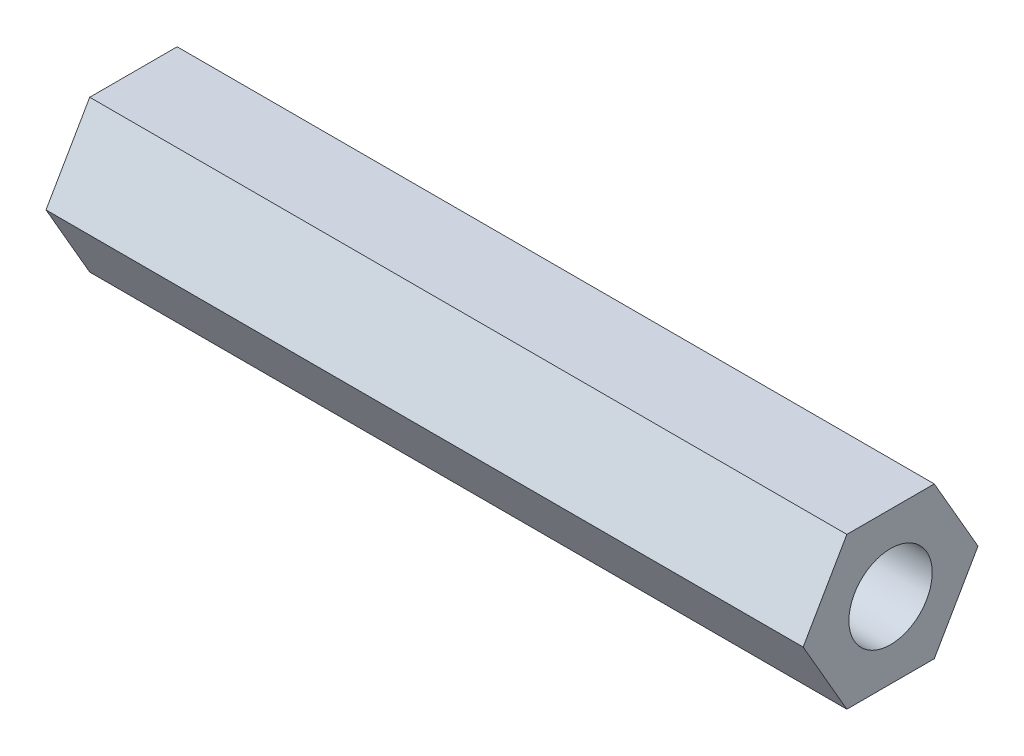
SolidWorks part; units mm, degrees
ref_plane "前视基准面" through (0, 0, 0) normal (0, 0, 1) x (1, 0, 0)
ref_plane "上视基准面" through (0, 0, 0) normal (0, 1, 0) x (1, 0, 0)
ref_plane "右视基准面" through (0, 0, 0) normal (1, 0, 0) x (0, 0, -1)
other "Configuration Table"
sketch "草图1" plane through (0, 0, 0) normal (1, 0, 0) x (0, 0, -1)
  line L1 (3.4641, 0) -> (1.7321, 3)
  line L2 (1.7321, 3) -> (-1.7321, 3)
  line L3 (-1.7321, 3) -> (-3.4641, 0)
  line L4 (-3.4641, 0) -> (-1.7321, -3)
  line L5 (-1.7321, -3) -> (1.7321, -3)
  line L6 (1.7321, -3) -> (3.4641, 0)
  circle A0 centre (0, 0) radius 3 construction
  dimension "D1" = 6
extrude "凸台-拉伸1" add sketch "草图1" along normal blind 30
hole_wizard "M4 螺纹孔1" positions "草图3" profile "草图4" tap size "M4" standard "GB" end condition through all
sketch "草图3" plane through (0, 0, 0) normal (-1, 0, 0) x (0, 0, 1)
  point P0 (0, 0)
sketch "草图4" plane through (0, 0, 0) normal (0, 1, 0) x (0, 0, 1)
  line L0 (0, 0) -> (0, 30)
  line L1 (0, 30) -> (1.65, 30)
  line L2 (1.65, 30) -> (1.65, 0)
  line L5 (1.65, 0) -> (0, 0)
  line L11 (0, -6.35) -> (0, 107.95) construction
  dimension "通孔螺纹孔钻头直径" = 3.3
  dimension "通孔螺纹孔钻头深度" = 30
cosmetic thread "孔螺蚊线1" parameters "D2"=4
